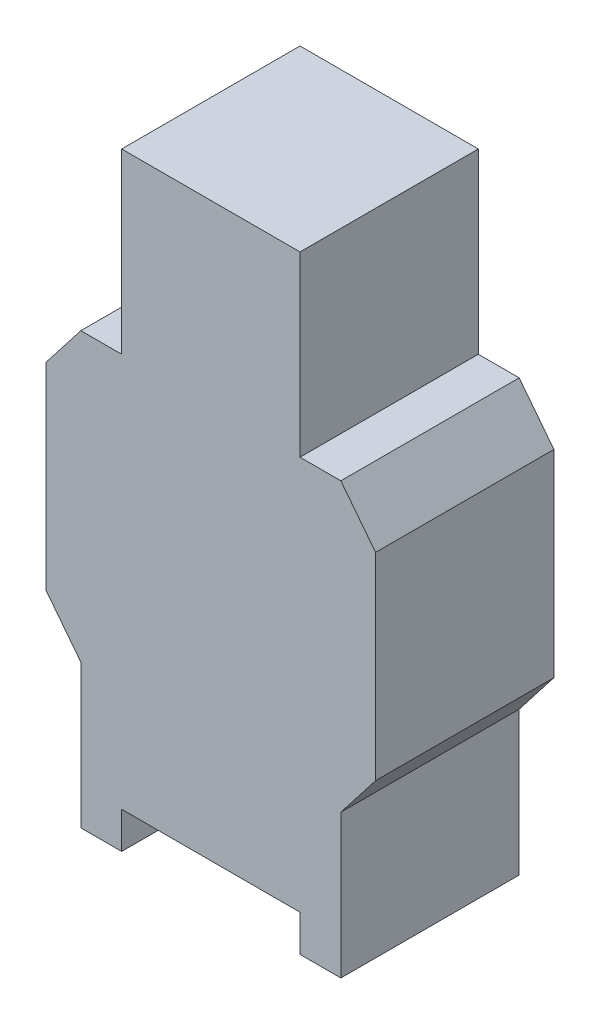
SolidWorks part; units mm, degrees
ref_plane "Front Plane" through (0, 0, 0) normal (0, 0, 1) x (1, 0, 0)
ref_plane "Top Plane" through (0, 0, 0) normal (0, 1, 0) x (1, 0, 0)
ref_plane "Right Plane" through (0, 0, 0) normal (1, 0, 0) x (0, 0, -1)
sketch "Sketch1" plane through (0, 0, 0) normal (0, 0, 1) x (1, 0, 0)
  line L0 (1.524, 0.019) -> (1.524, 1.0934)
  line L1 (1.8731, 1.2462) -> (2.1698, 1.6278)
  line L2 (2.1698, 1.6278) -> (2.1698, 3.3174)
  line L3 (1.8731, 1.2462) -> (1.8731, 0.019)
  line L4 (1.8731, 0.019) -> (1.524, 0.019)
  line L5 (1.524, 0.3314) -> (0, 0.3314)
  line L6 (0.762, 0.3314) -> (0.762, -0.5768) construction
  line L7 (2.1698, 2.4726) -> (2.8353, 2.4726) construction
  line L8 (1.8731, 3.699) -> (2.1698, 3.3174)
  line L9 (0.762, 5.2185) -> (0.762, 3.699) construction
  line L10 (0, 5.2185) -> (0, 3.699)
  line L11 (-0.3491, 3.699) -> (-0.6458, 3.3174)
  line L12 (-0.3491, 1.2462) -> (-0.3491, 0.019)
  line L13 (-0.6458, 1.6278) -> (-0.6458, 3.3174)
  line L14 (-0.3491, 1.2462) -> (-0.6458, 1.6278)
  line L15 (-0.3491, 0.019) -> (0, 0.019)
  line L16 (0, 0.3314) -> (0, 0.019)
  line L17 (0, 5.2185) -> (1.524, 5.2185)
  line L18 (1.524, 5.2185) -> (1.524, 3.699)
  line L19 (1.524, 3.699) -> (1.8731, 3.699)
  line L20 (-0.3491, 3.699) -> (0, 3.699)
  dimension "D1" = 0.762
  dimension "D2" = 0.762
extrude "Boss-Extrude1" add sketch "Sketch1" along normal blind 1.524
